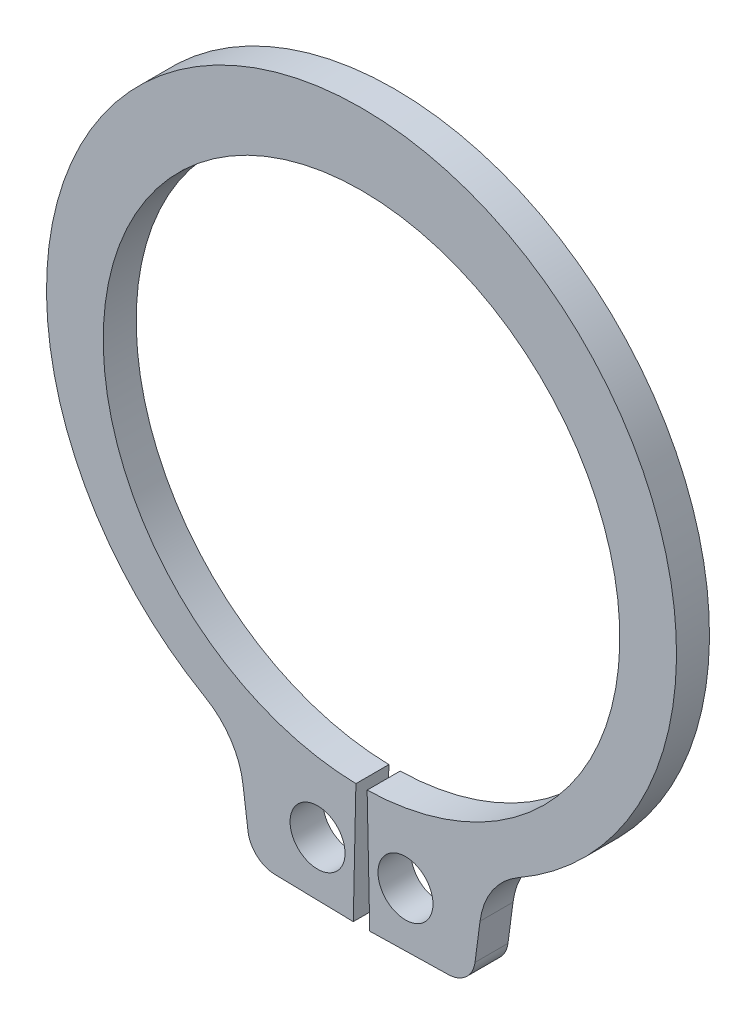
SolidWorks part; units mm, degrees
ref_plane "Plane1" through (0, 0, 0) normal (0, 0, 1) x (1, 0, 0)
ref_plane "Plane2" through (0, 0, 0) normal (0, 1, 0) x (1, 0, 0)
ref_plane "Plane3" through (0, 0, 0) normal (1, 0, 0) x (0, 0, -1)
sketch "Clipboard" plane through (0, 0, 0) normal (0, 0, 1) x (1, 0, 0)
  line L0 (0, 0) -> (1.3, 0)
  line L1 (0, 0) -> (0, 0.8)
  line L2 (0, 0) -> (0, -2.2)
  circle A0 centre (0, 0) radius 0.5
  circle A1 centre (0, 0) radius 5
  dimension "HoleDia" = 1
  dimension "ShaftDia" = 10
  dimension "LargeSection" = 1.3
  dimension "SmallSection" = 0.8
  dimension "LugSection" = 2.2
sketch "BodySke" plane through (0, 0, 0) normal (0, 0, 1) x (1, 0, 0)
  line L0 (-1.5431, 0) -> (1.5431, 0) construction
  line L1 (0, 0) -> (0, 6) construction
  line L2 (0.1022, -4.6989) -> (0.15, -6.8984)
  line L3 (-0.1022, -4.6989) -> (-0.15, -6.8984)
  line L4 (0, 0) -> (3.5443, -5.9201) construction
  line L5 (0, 0) -> (-3.5443, -5.9201) construction
  line L6 (0.15, -6.8984) -> (1.5802, -6.8673)
  line L7 (2.1566, -5.7375) -> (2.0651, -6.4327)
  line L8 (-2.1566, -5.7375) -> (-2.0651, -6.4327)
  line L9 (-0.15, -6.8984) -> (-1.5802, -6.8673)
  circle A0 centre (0, 0) radius 4.7 construction
  arc A1 (0.1022, -4.6989) -> (-0.1022, -4.6989) centre (0, 0) ccw
  arc A2 (2.8251, -4.719) -> (-2.8251, -4.719) centre (0, 0.2682) ccw construction
  arc A3 (0.15, -6.8984) -> (1.7279, -6.6801) centre (0, 0) ccw construction
  arc A4 (2.8486, -4.7056) -> (2.1566, -5.7375) centre (3.5443, -5.9201) ccw
  arc A5 (-2.1566, -5.7375) -> (-2.8486, -4.7056) centre (-3.5443, -5.9201) ccw
  arc A6 (-1.7279, -6.6801) -> (-0.15, -6.8984) centre (0, 0) ccw construction
  arc A7 (2.8486, -4.7056) -> (-2.8486, -4.7056) centre (0, 0.2682) ccw
  arc A8 (-2.1832, -5.535) -> (2.1832, -5.535) centre (0, 0) ccw construction
  circle A9 centre (0.8, -5.896) radius 0.5
  circle A10 centre (-0.8, -5.896) radius 0.5
  arc A11 (2.0651, -6.4327) -> (1.5802, -6.8673) centre (1.5693, -6.3674) cw
  arc A12 (-2.0651, -6.4327) -> (-1.5802, -6.8673) centre (-1.5693, -6.3674) ccw
  point P28 (2.0443, -6.5902)
  point P31 (-2.0443, -6.5902)
  dimension "GrooveDia" = 9.4
  dimension "D3" = 0.5
  dimension "LugRad" = 6.9
  dimension "HoleOffsetRad" = 5.95
  dimension "HoleDia" = 1
  dimension "D2" = 15
  dimension "LargeRad" = 6
  dimension "SmallRad" = 5.5
  dimension "Gap" = 0.3
  dimension "SmallAngle" = 61.816
  dimension "HoleSpacing" = 1.6
extrude "Body" add sketch "BodySke" against normal blind 0.6
sketch "NotSke" plane through (0, 0, 0) normal (0, 0, 1) x (1, 0, 0)
  line L0 (0.8, -5.396) -> (0.8, -6.396)
  line L1 (0.8, -6.396) -> (-0.8, -6.396)
  line L2 (-0.8, -6.396) -> (-0.8, -5.396)
  line L3 (-0.8, -5.396) -> (0.8, -5.396)
  circle A0 centre (0.8, -5.896) radius 0.5 construction
  circle A1 centre (-0.8, -5.896) radius 0.5 construction
extrude "Notch" [suppressed] cut sketch "NotSke" against normal through all
equation "' \"ShaftDia@Clipboard\" = 4"
equation "' \"Thickness@Body\" = 0.25"
equation "' \"GrooveDia@BodySke\" = 3.8"
equation "' \"LugSection@Clipboard\" = 1.35"
equation "' \"LargeSection@Clipboard\" = 0.65"
equation "' \"SmallSection@Clipboard\" = 0.4"
equation "' \"HoleDia@Clipboard\" = 0.6"
equation "' \"ShaftDia@Clipboard\" = 15"
equation "' \"Thickness@Body\" = 0.9"
equation "' \"GrooveDia@BodySke\" = 14.15"
equation "' \"LugSection@Clipboard\" = 2.8"
equation "' \"LargeSection@Clipboard\" = 1.8"
equation "' \"SmallSection@Clipboard\" = 1.05"
equation "' \"HoleDia@Clipboard\" = 1.2"
equation "\"Gap@BodySke\" =  \"Thickness@Body\" / 2"
equation "\"LargeRad@BodySke\" =  \"GrooveDia@BodySke\" / 2 +  \"LargeSection@Clipboard\""
equation "\"SmallRad@BodySke\" =  \"GrooveDia@BodySke\" / 2 +  \"SmallSection@Clipboard\""
equation "\"LugRad@BodySke\" = \"GrooveDia@BodySke\" / 2 + \"LugSection@Clipboard\""
equation "\"HoleOffsetRad@BodySke\" = (  \"ShaftDia@Clipboard\" / 2 + \"LugRad@BodySke\" ) / 2"
equation "\"HoleSpacing@BodySke\" = \"Gap@BodySke\"  * 2 +  \"HoleDia@Clipboard\""
equation "\"HoleDia@BodySke\" =  \"HoleDia@Clipboard\""
equation "\"SmallAngle@BodySke\" = atn(\"HoleSpacing@BodySke\" / 2 / sqr(\"HoleOffsetRad@BodySke\"  * \"HoleOffsetRad@BodySke\" - (\"HoleSpacing@BodySke\" / 2) * (\"HoleSpacing@BodySke\" / 2) ))  * 8 * ( 180 / 3.141593)"
